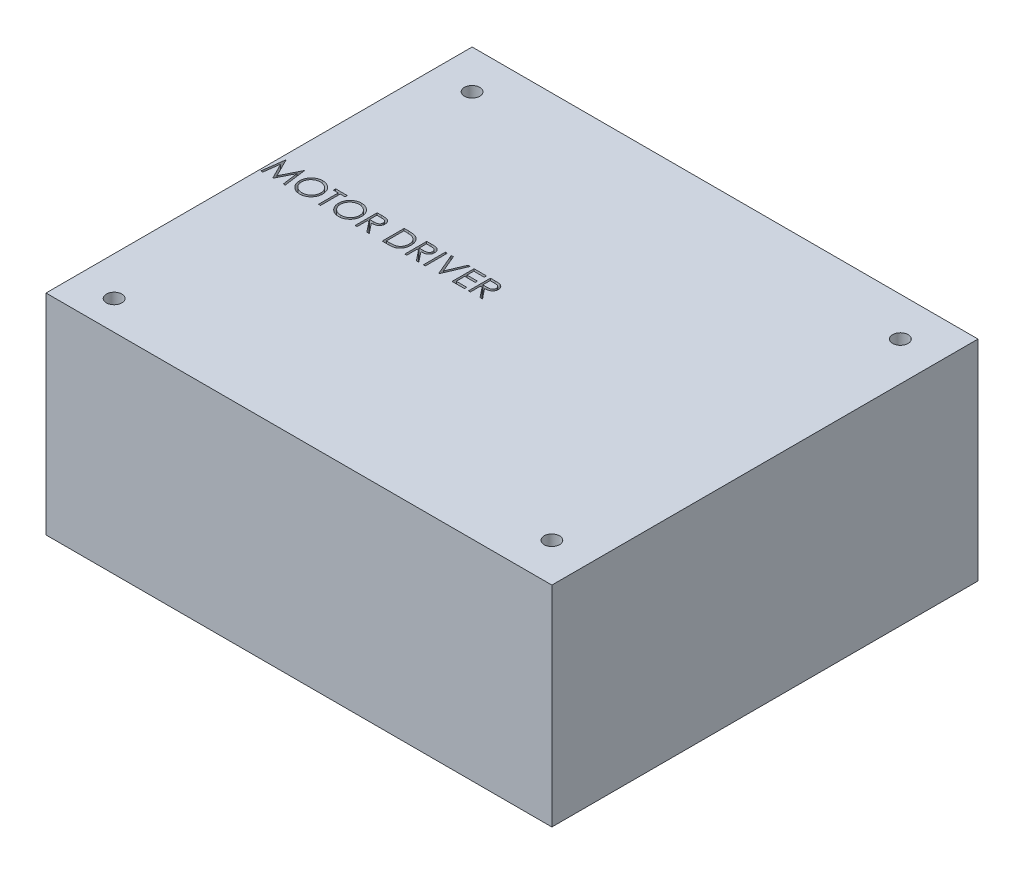
SolidWorks part; units mm, degrees
ref_plane "Front Plane" through (0, 0, 0) normal (0, 0, 1) x (1, 0, 0)
ref_plane "Top Plane" through (0, 0, 0) normal (0, 1, 0) x (1, 0, 0)
ref_plane "Right Plane" through (0, 0, 0) normal (1, 0, 0) x (0, 0, -1)
sketch "Sketch1" plane through (0, 0, 0) normal (0, 1, 0) x (1, 0, 0)
  line L1 (0, 0) -> (80.56, 0)
  line L2 (0, 0) -> (0, 67.86)
  line L3 (0, 67.86) -> (80.56, 67.86)
  line L4 (80.56, 0) -> (80.56, 67.86)
  dimension "D1" = 80.56
  dimension "D2" = 67.86
extrude "Boss-Extrude1" add sketch "Sketch1" along normal blind 33.37 contours L2 L1 L4 L3
sketch "Sketch2" plane through (0, 33.37, 0) normal (0, 1, 0) x (1, 0, 0)
  line L0 (0, 0) -> (0, 67.86) construction
  line L1 (0, 67.86) -> (80.56, 67.86) construction
  line L2 (80.56, 0) -> (80.56, 67.86) construction
  line L3 (0, 0) -> (80.56, 0) construction
  circle A0 centre (6.18, 61.68) radius 1.23
  circle A1 centre (6.18, 4.6703) radius 1.23
  circle A2 centre (74.38, 6.18) radius 1.23
  circle A3 centre (74.38, 61.68) radius 1.23
  dimension "D1" = 2.46
  dimension "D2" = 2.46
  dimension "D3" = 2.46
  dimension "D4" = 2.46
  dimension "D5" = 6.18
  dimension "D6" = 6.18
  dimension "D7" = 6.18
  dimension "D8" = 6.18
  dimension "D9" = 6.18
  dimension "D10" = 6.18
  dimension "D11" = 6.18
extrude "Cut-Extrude1" cut sketch "Sketch2" against normal through all
sketch "Sketch3" plane through (0, 33.37, 0) normal (0, 1, 0) x (1, 0, 0)
  line L0 (0, 33.93) -> (80.56, 33.93) construction
  line L1 (0, 0) -> (0, 67.86) construction
  line L2 (80.56, 0) -> (80.56, 67.86) construction
  text T0 "MOTOR DRIVER\r\n"
extrude "Cut-Extrude2" cut sketch "Sketch3" against normal through all
